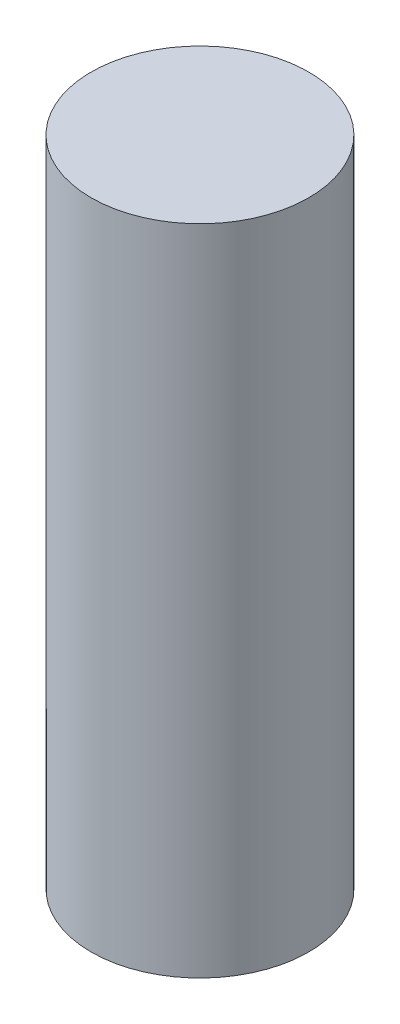
SolidWorks part; units mm, degrees
ref_plane "Front Plane" through (0, 0, 0) normal (0, 0, 1) x (1, 0, 0)
ref_plane "Top Plane" through (0, 0, 0) normal (0, 1, 0) x (1, 0, 0)
ref_plane "Right Plane" through (0, 0, 0) normal (1, 0, 0) x (0, 0, -1)
sketch "Sketch1" plane through (0, 0, 0) normal (0, 1, 0) x (1, 0, 0)
  circle A0 centre (0, 0) radius 1
  dimension "D1" = 2
extrude "Boss-Extrude1" add sketch "Sketch1" along normal blind 6
